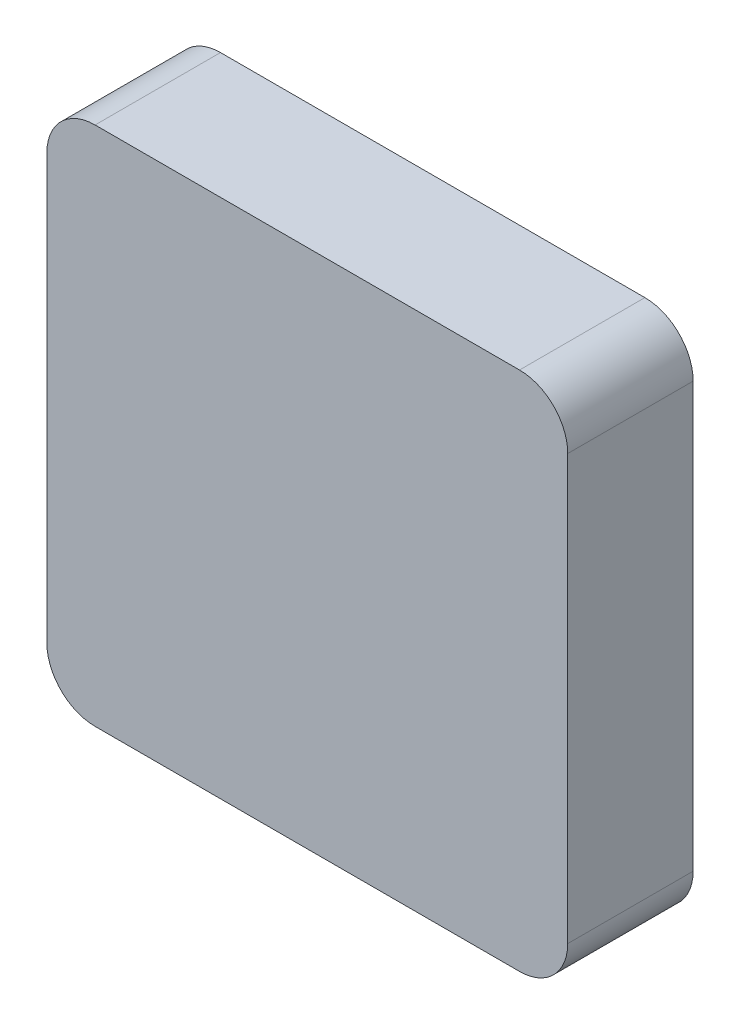
SolidWorks part; units mm, degrees
ref_plane "Plan de face" through (0, 0, 0) normal (0, 0, 1) x (1, 0, 0)
ref_plane "Plan de dessus" through (0, 0, 0) normal (0, 1, 0) x (1, 0, 0)
ref_plane "Plan de droite" through (0, 0, 0) normal (1, 0, 0) x (0, 0, -1)
sketch "Esquisse1" plane through (0, 0, 0) normal (0, 0, 1) x (1, 0, 0)
  line L0 (0, 0) -> (54, 0)
  line L1 (54, 0) -> (54, -54)
  line L2 (54, -54) -> (0, -54)
  line L3 (0, -54) -> (0, 0)
  dimension "D1" = 54
  dimension "D2" = 54
  dimension "D3" = 54
  dimension "D4" = 54
extrude "Boss.-Extru.1" add sketch "Esquisse1" along normal blind 13
fillet "Congé2" radius 5 4 edges at (0, 0, 6.5) (0, -54, 6.5) (54, -54, 6.5) (54, 0, 6.5)
